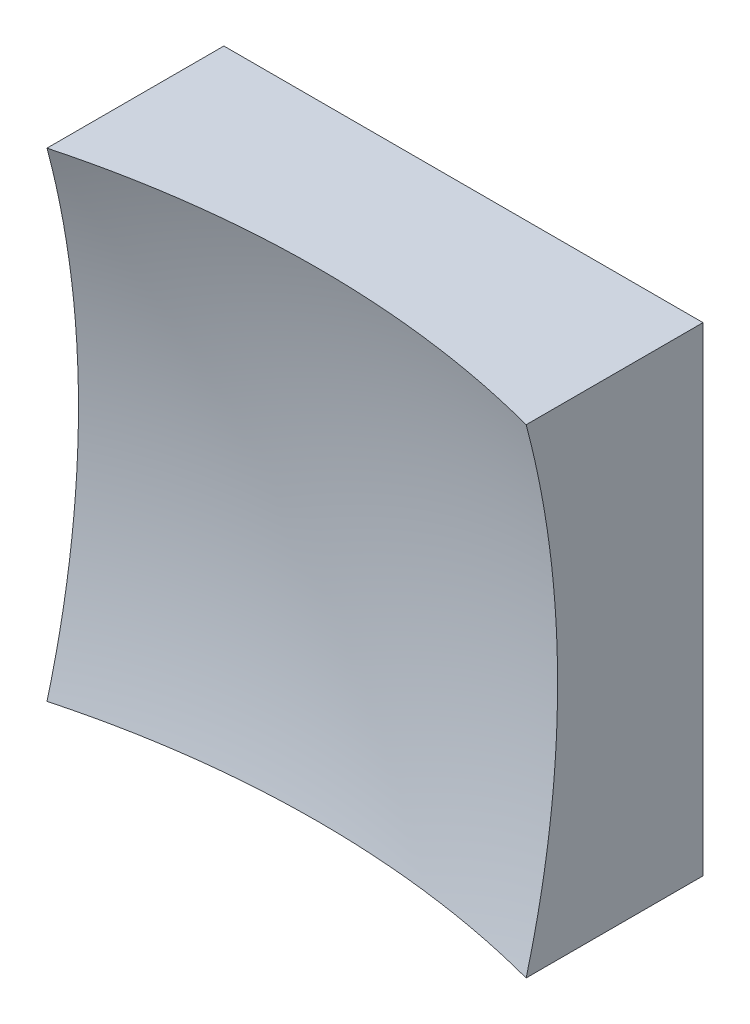
SolidWorks part; units mm, degrees
ref_plane "前视基准面" through (0, 0, 0) normal (0, 0, 1) x (1, 0, 0)
ref_plane "上视基准面" through (0, 0, 0) normal (0, 1, 0) x (1, 0, 0)
ref_plane "右视基准面" through (0, 0, 0) normal (1, 0, 0) x (0, 0, -1)
sketch "草图1" plane through (0, 0, 0) normal (0, 0, 1) x (1, 0, 0)
  line L1 (-12.5, 12.5) -> (12.5, 12.5)
  line L2 (-12.5, 12.5) -> (-12.5, -12.5)
  line L3 (-12.5, -12.5) -> (12.5, -12.5)
  line L4 (12.5, 12.5) -> (12.5, -12.5)
  line L5 (-12.5, 12.5) -> (12.5, -12.5) construction
  line L6 (-12.5, -12.5) -> (12.5, 12.5) construction
  point P0 (0, 0)
  dimension "D1" = 25
  dimension "D2" = 25
extrude "凸台-拉伸1" add sketch "草图1" along normal blind 20 contours L2 L3 L4 L1
sketch "草图2" plane through (0, 0, 0) normal (0, 1, 0) x (1, 0, 0)
  line L0 (-7.4603, -6) -> (7.3192, -6) construction
  line L1 (0, 0) -> (0, -12.1749) construction
  line L2 (48.7423, -44.8559) -> (0, -44.8559)
  line L3 (0, -44.8559) -> (0, -6)
  arc A1 (48.7423, -44.8559) -> (0, -6) centre (0, -56) ccw
  dimension "D2" = 100
  dimension "D1" = 6
revolve "切除-旋转2" cut sketch "草图2" angle 360 about L3
